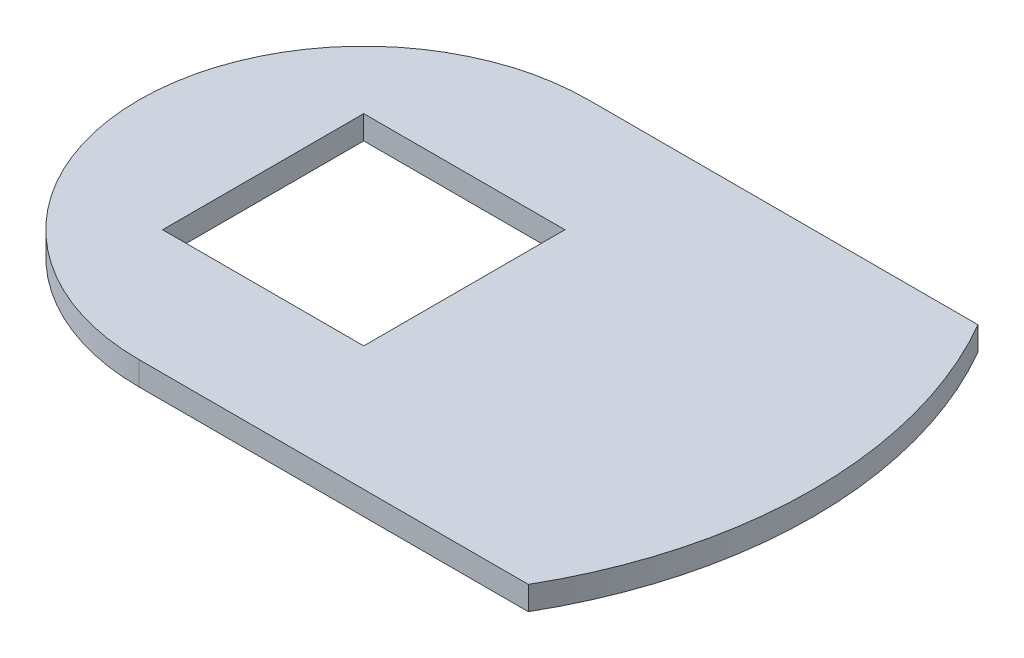
SolidWorks part; units mm, degrees
ref_plane "Ebene vorne" through (0, 0, 0) normal (0, 0, 1) x (1, 0, 0)
ref_plane "Ebene oben" through (0, 0, 0) normal (0, 1, 0) x (1, 0, 0)
ref_plane "Ebene rechts" through (0, 0, 0) normal (1, 0, 0) x (0, 0, -1)
sketch "Skizze1" plane through (0, 0, 0) normal (0, 1, 0) x (1, 0, 0)
  line L0 (0, 9.5) -> (16.4545, 9.5)
  line L1 (-4.25, 4.25) -> (4.25, 4.25)
  line L2 (-4.25, 4.25) -> (-4.25, -4.25)
  line L3 (-4.25, -4.25) -> (4.25, -4.25)
  line L4 (4.25, 4.25) -> (4.25, -4.25)
  line L5 (-4.25, 4.25) -> (4.25, -4.25) construction
  line L6 (-4.25, -4.25) -> (4.25, 4.25) construction
  line L7 (0, -9.5) -> (16.4545, -9.5)
  circle A0 centre (0, 0) radius 9.5 construction
  circle A1 centre (0, 0) radius 19 construction
  arc A2 (0, 9.5) -> (0, -9.5) centre (0, 0) ccw
  arc A3 (16.4545, -9.5) -> (16.4545, 9.5) centre (0, 0) ccw
  point P0 (0, 0)
  dimension "D2" = 19
  dimension "D3" = 38
  dimension "D1" = 8.5
extrude "Aufsatz-Linear austragen1" add sketch "Skizze1" along normal blind 1 contours L7 A3 L0 A2 L1 L4 L3 L2
